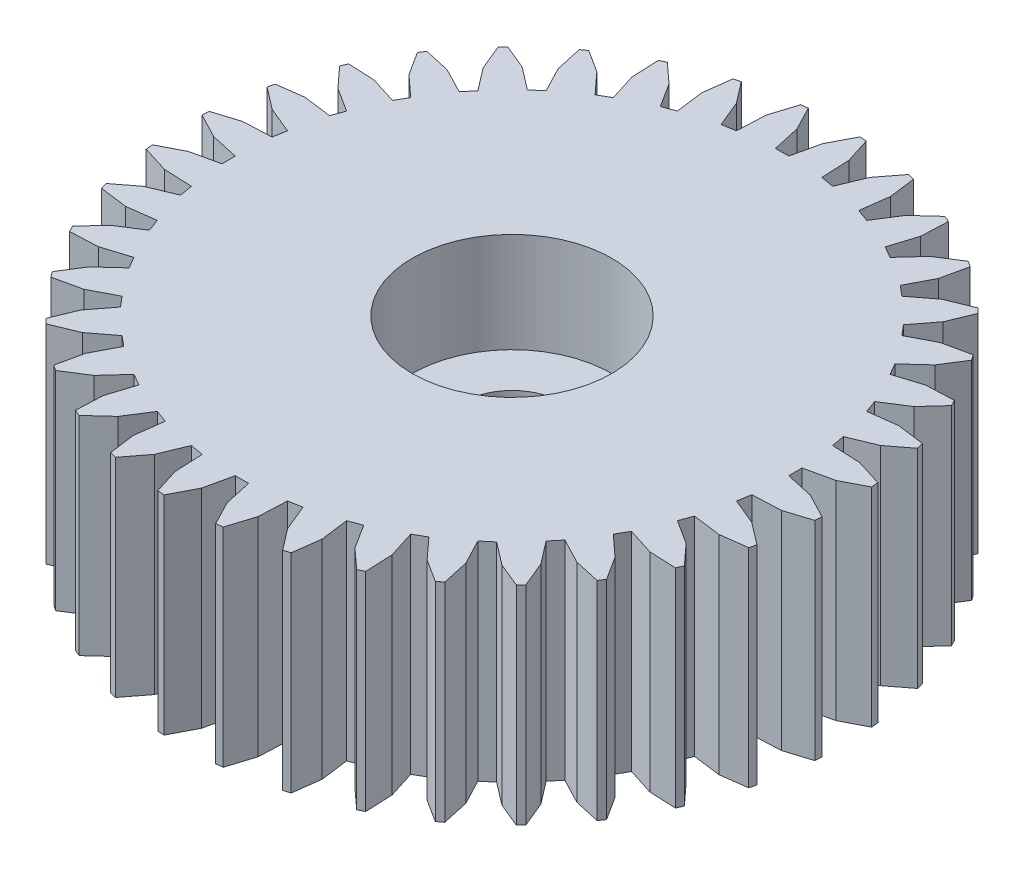
SolidWorks part; units mm, degrees
ref_plane "Front Plane" through (0, 0, 0) normal (0, 0, 1) x (1, 0, 0)
ref_plane "Top Plane" through (0, 0, 0) normal (0, 1, 0) x (1, 0, 0)
ref_plane "Right Plane" through (0, 0, 0) normal (1, 0, 0) x (0, 0, -1)
sketch "Sketch1" plane through (0, 0, 0) normal (0, 1, 0) x (1, 0, 0)
  circle A0 centre (0, 0) radius 10.0584
  dimension "D1" = 20.1168
extrude "Boss-Extrude1" add sketch "Sketch1" along normal blind 6.35
sketch "Sketch2" plane through (0, 6.35, 0) normal (0, 1, 0) x (1, 0, 0)
  circle A0 centre (0, 0) radius 1.524
  dimension "D1" = 3.048
extrude "Cut-Extrude1" cut sketch "Sketch2" against normal through all
sketch "Sketch3" plane through (0, 6.35, 0) normal (0, 1, 0) x (1, 0, 0)
  circle A0 centre (0, 0) radius 3.048
  dimension "D1" = 6.096
extrude "Cut-Extrude2" cut sketch "Sketch3" against normal blind 3.048
sketch "Sketch4" plane through (0, 0, 0) normal (0, -1, 0) x (1, 0, 0)
  line L0 (-0.9927, -10.0584) -> (-0.4064, -8.4474) construction
  line L1 (0, 0) -> (0, -10.0584) construction
  line L2 (-0.4064, -8.4474) -> (0, -8.4474)
  line L3 (0, -8.4474) -> (0.5863, -10.0584) construction
  line L4 (-0.9927, -10.0584) -> (-0.5935, -9.2915)
  line L5 (-0.5935, -9.2915) -> (-0.4064, -8.4474)
  line L6 (0, -8.4474) -> (0.1871, -9.2915)
  line L7 (0.1871, -9.2915) -> (0.5863, -10.0584)
  line L9 (0.5863, -10.0584) -> (0.9927, -10.0584) construction
  circle A0 centre (0, 0) radius 10.0584 construction
  dimension "D1" = 70
  dimension "D2" = 70
  dimension "D3" = 165
  dimension "D4" = 165
extrude "Cut-Extrude3" cut sketch "Sketch4" against normal through all flip side to cut
pattern_circular "CirPattern1" count 36 over 360 about axis through (0, 0, 0) along (0, 1, 0) of "Cut-Extrude3"
sketch "Pitch Dia" plane through (0, 0, 0) normal (0, -1, 0) x (1, 0, 0)
  circle A0 centre (0, 0) radius 9.525
  dimension "D1" = 19.05
sketch "Angle Indicator" plane through (0, 0, 0) normal (0, -1, 0) x (1, 0, 0)
  line L0 (0, 6.5078) -> (0, 0) construction
